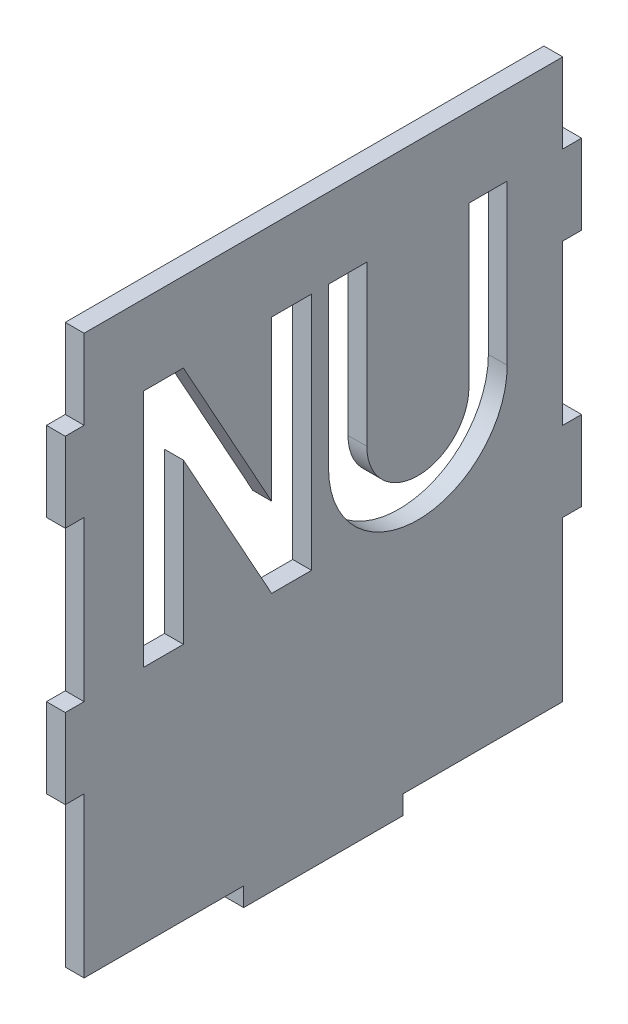
SolidWorks part; units mm, degrees
ref_plane "Front Plane" through (0, 0, 0) normal (0, 0, 1) x (1, 0, 0)
ref_plane "Top Plane" through (0, 0, 0) normal (0, 1, 0) x (1, 0, 0)
ref_plane "Right Plane" through (0, 0, 0) normal (1, 0, 0) x (0, 0, -1)
sketch "Sketch1" plane through (0, 0, 0) normal (1, 0, 0) x (0, 0, -1)
  line L0 (-38.1, -17.2847) -> (-38.1, -20.8153)
  line L1 (38.1, 6.35) -> (38.1, 31.75)
  line L2 (-38.1, 6.35) -> (-38.1, 31.75)
  line L3 (-38.1, -31.75) -> (-12.7, -31.75)
  line L4 (-41.1, 44.45) -> (-38.1, 44.45)
  line L5 (0, -20.8153) -> (0, -42.0936) construction
  line L6 (38.1, -17.2847) -> (38.1, -20.8153)
  line L7 (12.7, -31.75) -> (38.1, -31.75)
  line L8 (38.1, 31.75) -> (41.1, 31.75)
  line L9 (-12.7, -31.75) -> (-12.7, -34.75)
  line L10 (-12.7, -34.75) -> (12.7, -34.75)
  line L11 (12.7, -31.75) -> (12.7, -34.75)
  line L12 (41.1, 31.75) -> (41.1, 44.45)
  line L13 (-38.1, 44.45) -> (-38.1, 57.15)
  line L14 (-41.1, 44.45) -> (-41.1, 31.75)
  line L15 (-41.1, 31.75) -> (-38.1, 31.75)
  line L16 (-38.1, -20.8153) -> (-38.1, -31.75)
  line L17 (-38.1, 57.15) -> (38.1, 57.15)
  line L18 (38.1, 44.45) -> (41.1, 44.45)
  line L19 (38.1, 44.45) -> (38.1, 57.15)
  line L20 (-22.289, 44.45) -> (-8.2423, 19.05)
  line L21 (-38.1, -6.35) -> (-38.1, -17.2847)
  line L22 (-28.639, 44.45) -> (-22.289, 44.45)
  line L23 (38.1, -6.35) -> (38.1, -17.2847)
  line L24 (-28.639, 44.45) -> (-28.639, 6.35)
  line L25 (-28.639, 6.35) -> (-22.289, 6.35)
  line L26 (-38.1, 6.35) -> (-41.1, 6.35)
  line L27 (-1.8923, 44.45) -> (-1.8923, 6.35)
  line L28 (-8.2423, 19.05) -> (-8.2423, 44.45)
  line L29 (-38.1, -6.35) -> (-41.1, -6.35)
  line L30 (-22.289, 6.35) -> (-22.289, 31.75)
  line L31 (-22.289, 31.75) -> (-8.2423, 6.35)
  line L32 (-8.2423, 44.45) -> (-1.8923, 44.45)
  line L33 (-8.2423, 6.35) -> (-1.8923, 6.35)
  line L34 (23.1658, 44.45) -> (29.2618, 44.45)
  line L35 (29.2618, 44.45) -> (29.2618, 19.05)
  line L36 (23.1658, 44.45) -> (23.1658, 19.05)
  line L37 (6.9098, 44.45) -> (6.9098, 19.05)
  line L38 (0.8138, 44.45) -> (0.8138, 19.05)
  line L39 (38.1, -20.8153) -> (38.1, -31.75)
  line L40 (-41.1, 6.35) -> (-41.1, -6.35)
  line L41 (38.1, 6.35) -> (41.1, 6.35)
  line L43 (38.1, -6.35) -> (41.1, -6.35)
  line L44 (41.1, 6.35) -> (41.1, -6.35)
  line L46 (0.8138, 44.45) -> (6.9098, 44.45)
  arc A1 (0.8138, 19.05) -> (29.2618, 19.05) centre (15.0378, 19.05) ccw
  arc A2 (6.9098, 19.05) -> (23.1658, 19.05) centre (15.0378, 19.05) ccw
  dimension "D18" = 6.096
  dimension "D19" = 14.224
  dimension "D1" = 76.2
  dimension "D2" = 25.4
  dimension "D3" = 25.4
  dimension "D4" = 25.4
  dimension "D5" = 12.7
  dimension "D6" = 3
  dimension "D7" = 12.7
  dimension "D8" = 12.7
  dimension "D9" = 88.9
  dimension "D10" = 12.7
  dimension "D11" = 12.7
  dimension "D13" = 12.7
  dimension "D14" = 12.7
  dimension "D15" = 3
  dimension "D16" = 3
  dimension "D12" = 6.35
  dimension "D17" = 6.35
extrude "Boss-Extrude1" add sketch "Sketch1" along normal blind 3
